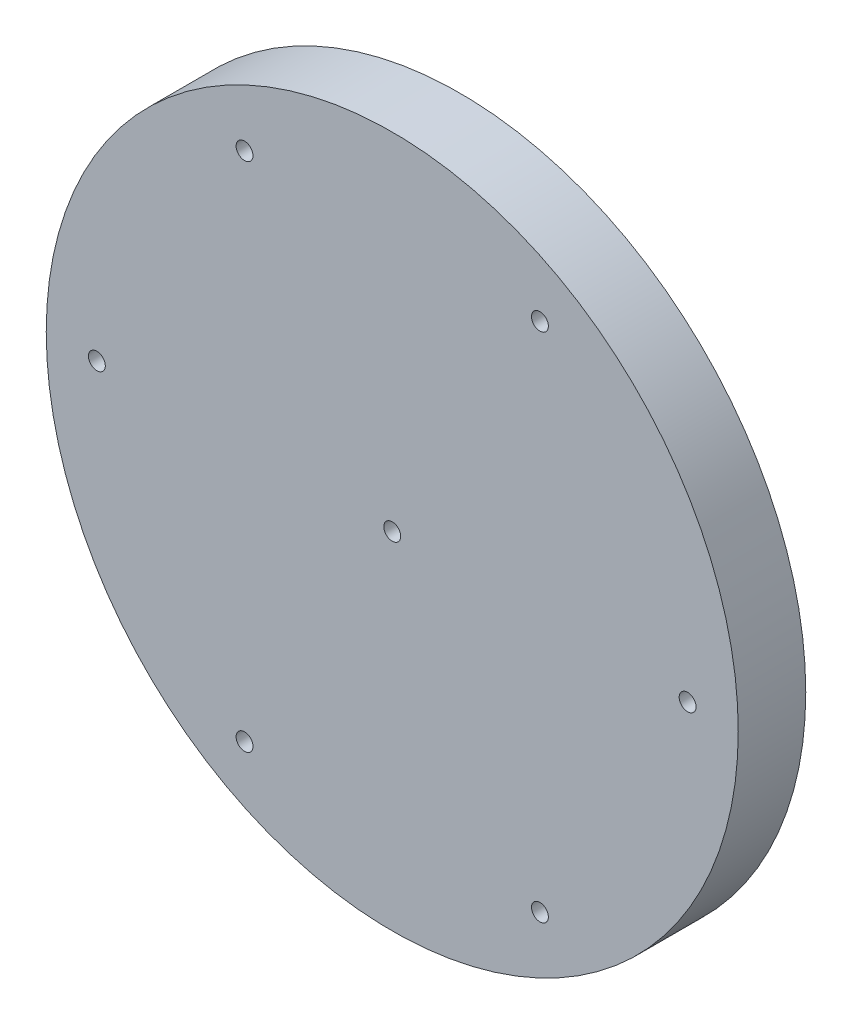
SolidWorks part; units mm, degrees
material "Acrylic (Medium-high impact)"
ref_plane "Front Plane" through (0, 0, 0) normal (0, 0, 1) x (1, 0, 0)
ref_plane "Top Plane" through (0, 0, 0) normal (0, 1, 0) x (1, 0, 0)
ref_plane "Right Plane" through (0, 0, 0) normal (1, 0, 0) x (0, 0, -1)
sketch "Model" plane through (0, 0, 0) normal (0, 0, 1) x (1, 0, 0)
  circle A224 centre (0, 0) radius 0.5
  circle A225 centre (17.5, 0) radius 0.5
  circle A226 centre (8.75, 15.1554) radius 0.5
  circle A227 centre (-8.75, 15.1554) radius 0.5
  circle A228 centre (-17.5, 0) radius 0.5
  circle A229 centre (-8.75, -15.1554) radius 0.5
  circle A230 centre (8.75, -15.1554) radius 0.5
  circle A231 centre (0, 0) radius 20.5
  dimension "D1" = 41
  dimension "D2" = 1
  dimension "D3" = 1
  dimension "D4" = 1
  dimension "D5" = 1
  dimension "D6" = 1
  dimension "D7" = 1
  dimension "D8" = 1
  dimension "D9" = 8.75
  dimension "D10" = 17.5
  dimension "D11" = 8.75
  dimension "D12" = 17.5
  dimension "D13" = 15.1554
  dimension "D14" = 15.1554
extrude "Boss-Extrude1" add sketch "Model" along normal blind 4
